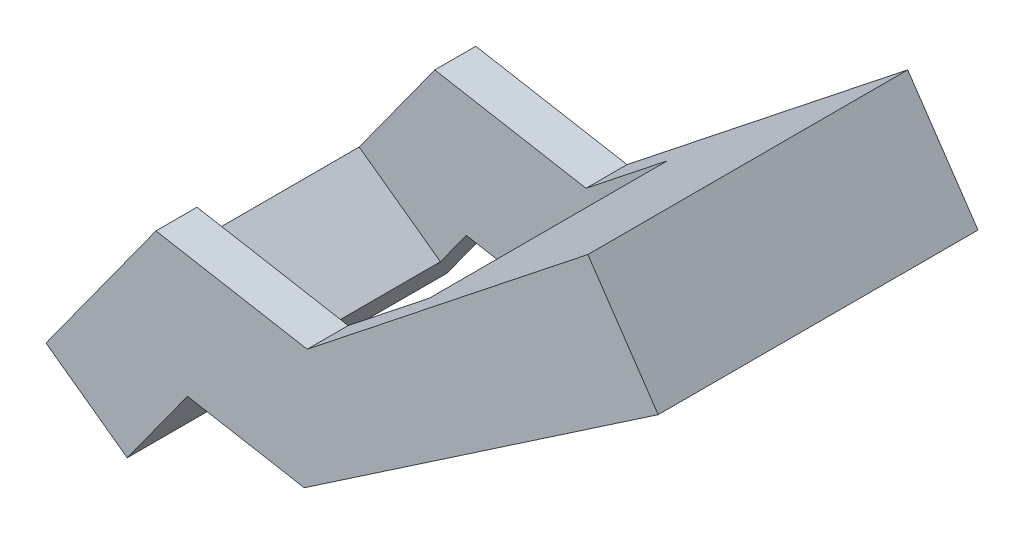
SolidWorks part; units mm, degrees
ref_plane "Front" through (0, 0, 0) normal (0, 0, 1) x (1, 0, 0)
ref_plane "Top" through (0, 0, 0) normal (0, 1, 0) x (1, 0, 0)
ref_plane "Right" through (0, 0, 0) normal (1, 0, 0) x (0, 0, -1)
sketch "Sketch1" plane through (0, 0, 0) normal (0, 0, 1) x (1, 0, 0)
  line L0 (3.0438, 8.1024) -> (39.9233, 1.5446)
  line L1 (39.9233, 1.5446) -> (108.3796, 55.7836)
  line L2 (108.3796, 55.7836) -> (125.5266, 30.5219)
  line L3 (125.5266, 30.5219) -> (39.2116, -28.0667)
  line L4 (39.2116, -28.0667) -> (10.7265, -23.0016)
  line L5 (10.7265, -23.0016) -> (-3.9668, -43.3248)
  line L6 (-3.9668, -43.3248) -> (-23.7805, -28.9999)
  line L7 (-23.7805, -28.9999) -> (3.0438, 8.1024)
  line L8 (126.6498, 28.8671) -> (107.2533, 57.4429) construction
  line L10 (10.7265, -23.0016) -> (-27.7535, -76.2256) construction
  line L11 (-59.8216, -78.8507) -> (3.0438, 8.1024) construction
extrude "Boss-Extrude1" add sketch "Sketch1" against normal blind 10
sketch "Sketch2" plane through (0, 0, -10) normal (0, 0, -1) x (-1, 0, 0)
  line L0 (-59.7128, 17.2241) -> (-74.2922, -4.2548)
  line L1 (-108.3796, 55.7836) -> (-39.9233, 1.5446) construction
  line L2 (-39.2116, -28.0667) -> (-125.5266, 30.5219) construction
  line L3 (-74.2922, -4.2548) -> (-125.5266, 30.5219)
  line L4 (-125.5266, 30.5219) -> (-108.3796, 55.7836) construction
  line L5 (-125.5266, 30.5219) -> (-108.3796, 55.7836)
  line L6 (-108.3796, 55.7836) -> (-59.7128, 17.2241)
  line L7 (23.7805, -28.9999) -> (3.9668, -43.3248)
  line L8 (3.9668, -43.3248) -> (-4.4202, -31.7242)
  line L9 (3.9668, -43.3248) -> (-10.7265, -23.0016) construction
  line L10 (-4.4202, -31.7242) -> (15.3934, -17.3993)
  line L11 (-3.0438, 8.1024) -> (23.7805, -28.9999) construction
  line L12 (15.3934, -17.3993) -> (23.7805, -28.9999)
extrude "Boss-Extrude2" add sketch "Sketch2" along a picked direction on the side of the normal blind 29
mirror "Mirror1" about plane through (0, 0, -39) normal (0, 0, 1) of "Boss-Extrude2", "Boss-Extrude1"
